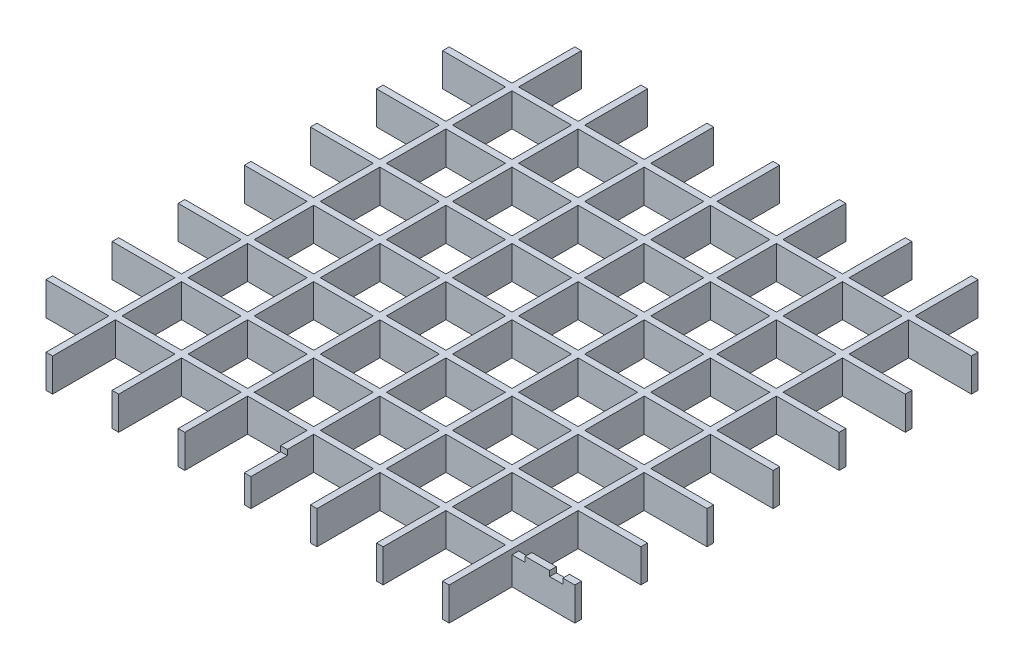
SolidWorks part; units mm, degrees
ref_plane "Front Plane" through (0, 0, 0) normal (0, 0, 1) x (1, 0, 0)
ref_plane "Top Plane" through (0, 0, 0) normal (0, 1, 0) x (1, 0, 0)
ref_plane "Right Plane" through (0, 0, 0) normal (1, 0, 0) x (0, 0, -1)
sketch "Sketch1" plane through (0, 0, 0) normal (0, 1, 0) x (1, 0, 0)
  line L1 (1.27, 101.6) -> (-1.27, 101.6)
  line L2 (1.27, 101.6) -> (1.27, -101.6)
  line L3 (1.27, -101.6) -> (-1.27, -101.6)
  line L4 (-1.27, 101.6) -> (-1.27, -101.6)
  line L5 (1.27, 101.6) -> (-1.27, -101.6) construction
  line L6 (1.27, -101.6) -> (-1.27, 101.6) construction
  point P0 (0, 0)
  dimension "D1" = 2.54
  dimension "D2" = 203.2
extrude "Boss-Extrude1" add sketch "Sketch1" along normal blind 12.7
pattern_linear "LPattern1" count 7 spacing 25.4 along (1, 0, 0) of "Boss-Extrude1"
sketch "Sketch2" plane through (0, 0, 0) normal (0, 1, 0) x (1, 0, 0)
  line L0 (76.2, 101.6) -> (76.2, 76.2) construction
  line L1 (77.47, 101.6) -> (74.93, 101.6) construction
  line L3 (-25.4, 74.93) -> (177.8, 74.93)
  line L4 (-25.4, 74.93) -> (-25.4, 77.47)
  line L5 (-25.4, 77.47) -> (177.8, 77.47)
  line L6 (177.8, 74.93) -> (177.8, 77.47)
  line L7 (-25.4, 74.93) -> (177.8, 77.47) construction
  line L8 (-25.4, 77.47) -> (177.8, 74.93) construction
  dimension "D1" = 2.54
  dimension "D2" = 203.2
  dimension "D3" = 25.4
extrude "Boss-Extrude2" add sketch "Sketch2" along normal blind 12.7
pattern_linear "LPattern2" count 7 spacing 25.4 along (0, 0, 1) of "Boss-Extrude2"
sketch "Sketch3" plane through (0, 12.7, 0) normal (0, 1, 0) x (1, 0, 0)
  line L5 (153.67, -77.47) -> (177.8, -77.47) construction
  line L6 (153.67, -74.93) -> (158.75, -74.93)
  line L7 (153.67, -74.93) -> (153.67, -77.47)
  line L8 (153.67, -77.47) -> (158.75, -77.47)
  line L9 (158.75, -74.93) -> (158.75, -77.47)
  line L10 (177.8, -74.93) -> (153.67, -74.93) construction
  line L11 (173.228, -74.93) -> (168.148, -74.93)
  line L12 (173.228, -74.93) -> (173.228, -77.47)
  line L13 (173.228, -77.47) -> (168.148, -77.47)
  line L14 (168.148, -74.93) -> (168.148, -77.47)
  line L15 (177.8, -77.47) -> (177.8, -74.93) construction
  line L16 (74.93, -77.47) -> (74.93, -101.6) construction
  line L17 (77.47, -101.6) -> (74.93, -101.6)
  line L18 (77.47, -101.6) -> (77.47, -87.63)
  line L19 (77.47, -87.63) -> (74.93, -87.63)
  line L20 (74.93, -101.6) -> (74.93, -87.63)
  dimension "D2" = 5.08
  dimension "D3" = 5.08
  dimension "D4" = 4.572
  dimension "D5" = 13.97
extrude "Cut-Extrude1" cut sketch "Sketch3" against normal blind 2.032
